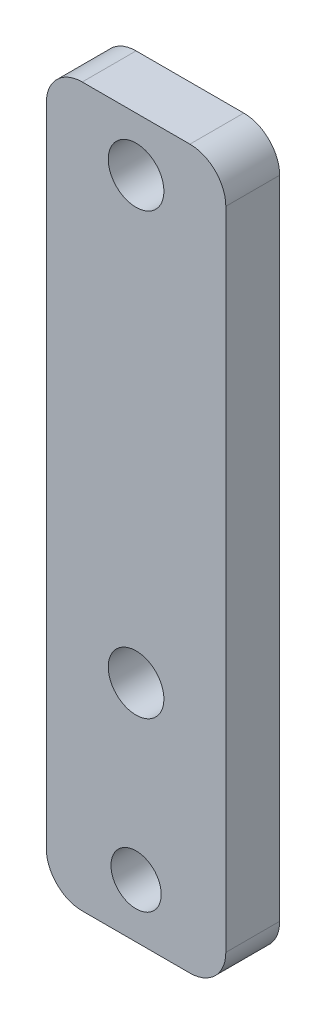
SolidWorks part; units mm, degrees
ref_plane "Plan de face" through (0, 0, 0) normal (0, 0, 1) x (1, 0, 0)
ref_plane "Plan de dessus" through (0, 0, 0) normal (0, 1, 0) x (1, 0, 0)
ref_plane "Plan de droite" through (0, 0, 0) normal (1, 0, 0) x (0, 0, -1)
sketch "Esquisse1" plane through (0, 0, 0) normal (0, 0, 1) x (1, 0, 0)
  line L1 (-5, -15) -> (5, -15)
  line L2 (-5, -15) -> (-5, 15)
  line L3 (-5, 15) -> (5, 15)
  line L4 (5, -15) -> (5, 15)
  line L5 (-5, -15) -> (5, 15) construction
  line L6 (-5, 15) -> (5, -15) construction
  circle A0 centre (0, 12) radius 1.55
  circle A1 centre (0, -12.5) radius 1.55
  point P0 (0, 0)
  dimension "D3" = 3.1
  dimension "D1" = 10
  dimension "D2" = 30
  dimension "D4" = 3
  dimension "D5" = 2.5
extrude "Boss.-Extru.1" add sketch "Esquisse1" along normal blind 3
sketch "Esquisse3" plane through (0, 0, 3) normal (0, 0, 1) x (1, 0, 0)
  line L0 (5, -15) -> (5, 15) construction
  line L1 (-5, -15) -> (5, -15)
  line L2 (-5, -15) -> (-5, -25)
  line L3 (-5, -25) -> (5, -25)
  line L4 (5, -15) -> (5, -25)
  circle A0 centre (0, -22) radius 1.4
  point P10 (0, -25)
  dimension "D2" = 2.8
  dimension "D1" = 10
  dimension "D3" = 3
extrude "Boss.-Extru.2" add sketch "Esquisse3" against normal blind 3
fillet "Congé1" radius 2 4 edges at (-5, -25, 1.5) (5, -25, 1.5) (-5, 15, 1.5) (5, 15, 1.5)
